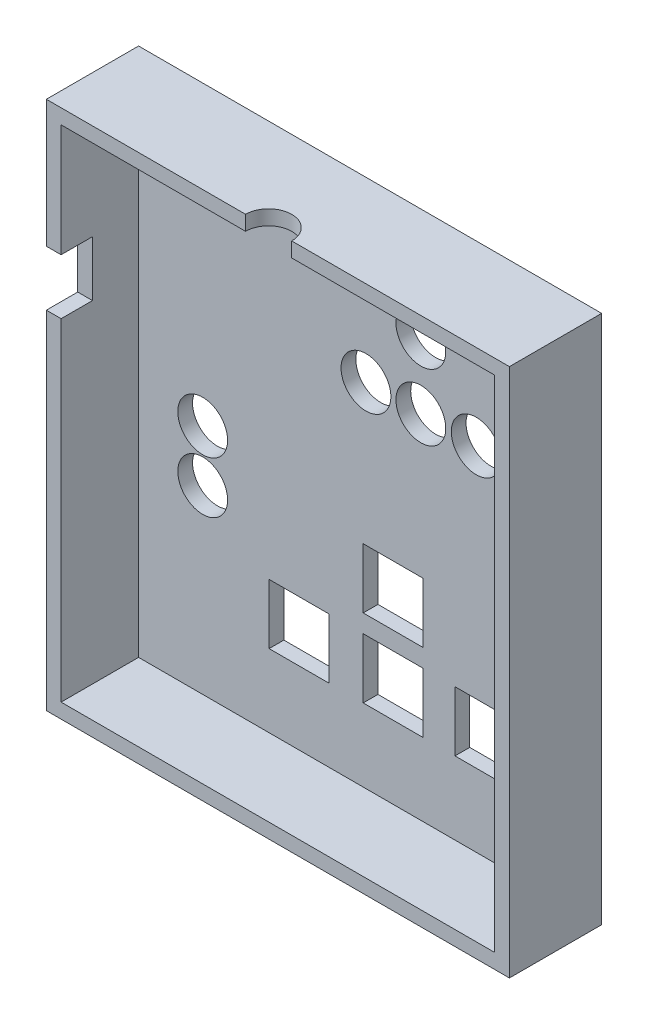
SolidWorks part; units mm, degrees
ref_plane "Płaszczyzna przednia" through (0, 0, 0) normal (0, 0, 1) x (1, 0, 0)
ref_plane "Płaszczyzna górna" through (0, 0, 0) normal (0, 1, 0) x (1, 0, 0)
ref_plane "Płaszczyzna prawa" through (0, 0, 0) normal (1, 0, 0) x (0, 0, -1)
sketch "Sketch1" plane through (0, 0, 0) normal (0, 0, 1) x (1, 0, 0)
  line L1 (0, -3.8533) -> (50.2, -3.8533)
  line L2 (0, -3.8533) -> (0, 53.5467)
  line L3 (0, 53.5467) -> (50.2, 53.5467)
  line L4 (50.2, -3.8533) -> (50.2, 53.5467)
  dimension "D1" = 50.2
  dimension "D2" = 57.4
extrude "Boss-Extrude1" add sketch "Sketch1" along normal blind 10
shell "Shell1" thickness 1.6
sketch "Sketch2" plane through (0, 0, 0) normal (0, 0, -1) x (-1, 0, 0)
  line L0 (0, -3.8533) -> (-50.2, -3.8533) construction
  line L1 (0, 53.5467) -> (0, -3.8533) construction
  line L2 (-50.2, -3.8533) -> (-50.2, 53.5467) construction
  circle A0 centre (-8.55, 17.3467) radius 2.7
  circle A1 centre (-8.55, 22.9467) radius 2.7
  circle A2 centre (-44.15, 35.8967) radius 2.7
  circle A3 centre (-26.25, 35.8967) radius 2.7
  circle A4 centre (-38.2, 35.8967) radius 2.7
  circle A5 centre (-32.2, 35.8967) radius 2.7
  circle A6 centre (-32.2, 43.0967) radius 2.7
  dimension "D1" = 5.4
  dimension "D2" = 21.2
  dimension "D4" = 5.4
  dimension "D5" = 8.55
  dimension "D6" = 5.6
  dimension "D7" = 5.4
  dimension "D8" = 5.4
  dimension "D9" = 5.4
  dimension "D10" = 5.4
  dimension "D11" = 6.05
  dimension "D12" = 12
  dimension "D13" = 18
  dimension "D14" = 23.95
  dimension "D15" = 39.75
  dimension "D16" = 39.75
  dimension "D17" = 39.75
  dimension "D18" = 39.75
  dimension "D19" = 5.4
  dimension "D20" = 18
  dimension "D21" = 46.95
  dimension "D3" = 8.55
extrude "Cut-Extrude1" cut sketch "Sketch2" against normal blind 10
sketch "Sketch3" plane through (0, 0, 0) normal (-1, 0, 0) x (0, 0, 1)
  line L0 (10, 53.5467) -> (10, -3.8533) construction
  line L1 (10, 39.7467) -> (6.6, 39.7467)
  line L2 (10, 39.7467) -> (10, 33.7467)
  line L3 (10, 33.7467) -> (6.6, 33.7467)
  line L4 (6.6, 39.7467) -> (6.6, 33.7467)
  line L5 (10, -3.8533) -> (0, -3.8533) construction
  dimension "D1" = 3.4
  dimension "D2" = 6
  dimension "D3" = 37.6
extrude "Cut-Extrude2" cut sketch "Sketch3" against normal blind 10
sketch "Sketch4" plane through (0, 53.5467, 0) normal (0, 1, 0) x (1, 0, 0)
  line L0 (0, -10) -> (0, 0) construction
  circle A0 centre (24.1, -10) radius 2.5
  dimension "D1" = 5
  dimension "D2" = 24.1
extrude "Cut-Extrude3" cut sketch "Sketch4" against normal blind 10
sketch "Sketch5" plane through (0, 0, 0) normal (0, 0, -1) x (-1, 0, 0)
  line L0 (0, -3.8533) -> (-50.2, -3.8533) construction
  line L1 (-35.9, 5.6467) -> (-42.4, 5.6467)
  line L2 (-35.9, 5.6467) -> (-35.9, 12.1467)
  line L3 (-35.9, 12.1467) -> (-42.4, 12.1467)
  line L4 (-42.4, 5.6467) -> (-42.4, 12.1467)
  line L5 (-50.2, -3.8533) -> (-50.2, 53.5467) construction
  line L7 (-25.95, 12.1467) -> (-32.45, 12.1467)
  line L8 (-25.95, 12.1467) -> (-25.95, 5.6467)
  line L9 (-25.95, 5.6467) -> (-32.45, 5.6467)
  line L10 (-32.45, 12.1467) -> (-32.45, 5.6467)
  line L11 (-15.75, 12.1467) -> (-22.25, 12.1467)
  line L12 (-15.75, 12.1467) -> (-15.75, 5.6467)
  line L13 (-15.75, 5.6467) -> (-22.25, 5.6467)
  line L14 (-22.25, 12.1467) -> (-22.25, 5.6467)
  line L15 (-25.95, 20.5967) -> (-32.45, 20.5967)
  line L16 (-25.95, 20.5967) -> (-25.95, 14.0967)
  line L17 (-25.95, 14.0967) -> (-32.45, 14.0967)
  line L18 (-32.45, 20.5967) -> (-32.45, 14.0967)
  dimension "D1" = 9.5
  dimension "D2" = 6.5
  dimension "D3" = 6.5
  dimension "D4" = 7.8
  dimension "D5" = 9.5
  dimension "D6" = 9.5
  dimension "D7" = 6.5
  dimension "D8" = 6.5
  dimension "D9" = 6.5
  dimension "D10" = 6.5
  dimension "D11" = 6.5
  dimension "D12" = 6.5
  dimension "D13" = 17.75
  dimension "D14" = 27.95
  dimension "D15" = 17.75
  dimension "D16" = 1.95
extrude "Cut-Extrude4" cut sketch "Sketch5" against normal blind 10
